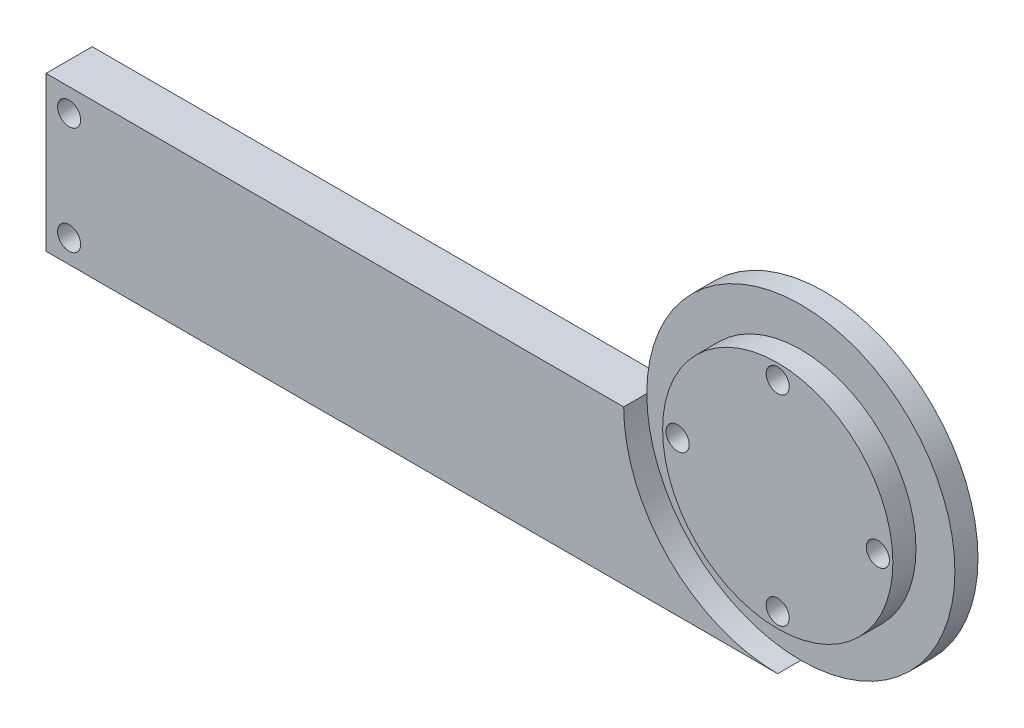
SolidWorks part; units mm, degrees
ref_plane "Plan de face" through (0, 0, 0) normal (0, 0, 1) x (1, 0, 0)
ref_plane "Plan de dessus" through (0, 0, 0) normal (0, 1, 0) x (1, 0, 0)
ref_plane "Plan de droite" through (0, 0, 0) normal (1, 0, 0) x (0, 0, -1)
sketch "Esquisse1" plane through (0, 0, 0) normal (0, 0, 1) x (1, 0, 0)
  line L1 (-45.5828, 28.0993) -> (32.9922, 28.0993)
  line L2 (-45.5828, 28.0993) -> (-45.5828, 8.0993)
  line L3 (-45.5828, 8.0993) -> (32.9922, 8.0993)
  line L4 (32.9922, 28.0993) -> (32.9922, 8.0993)
  circle A0 centre (32.9922, 28.0993) radius 20
  dimension "D3" = 40
  dimension "D1" = 0
  dimension "D2" = 20
  dimension "D4" = 0
extrude "Boss.-Extru.1" add sketch "Esquisse1" along normal blind 6 contours L4 A0 L1 | L1 A0 L4 | A0 L1 L2 L3
sketch "Esquisse4" plane through (0, 0, 6) normal (0, 0, 1) x (1, 0, 0)
  circle A0 centre (32.9922, 28.0993) radius 14.95
  arc A1 (32.9922, 8.0993) -> (12.9922, 28.0993) centre (32.9922, 28.0993) ccw construction
  circle A2 centre (32.9922, 28.0993) radius 20
  dimension "D1" = 0
  dimension "D2" = 29.9
extrude "Enlèv. mat.-Extru.2" cut sketch "Esquisse4" against normal blind 3
sketch "Esquisse5" plane through (0, 0, 6) normal (0, 0, 1) x (1, 0, 0)
  line L0 (-45.5828, 28.0993) -> (12.9922, 28.0993) construction
  line L1 (-45.5828, 8.0993) -> (-62.0028, 8.0993)
  line L2 (-45.5828, 8.0993) -> (-45.5828, 28.0993)
  line L3 (-45.5828, 28.0993) -> (-62.0028, 28.0993)
  line L4 (-62.0028, 8.0993) -> (-62.0028, 28.0993)
  dimension "D1" = 0
  dimension "D2" = 16.42
  dimension "D3" = 20
extrude "Boss.-Extru.2" add sketch "Esquisse5" against normal blind 6
sketch "Esquisse6" plane through (0, 0, 6) normal (0, 0, 1) x (1, 0, 0)
  circle A0 centre (32.9922, 28.0993) radius 13 construction
  circle A1 centre (32.9922, 28.0993) radius 14.95 construction
  circle A2 centre (32.9922, 41.0993) radius 1.5
  circle A3 centre (45.9922, 28.0993) radius 1.5
  circle A4 centre (32.9922, 15.0993) radius 1.5
  circle A5 centre (19.9922, 28.0993) radius 1.5
  dimension "D1" = 0
  dimension "D2" = 26
  dimension "D3" = 3
  dimension "D4" = 3
  dimension "D5" = 3
  dimension "D6" = 3
extrude "Enlèv. mat.-Extru.3" cut sketch "Esquisse6" against normal blind 10
sketch "Esquisse8" plane through (0, 0, 0) normal (0, 0, -1) x (-1, 0, 0)
  circle A0 centre (-32.9922, 28.0993) radius 20
  arc A1 (-12.9922, 28.0993) -> (-32.9922, 8.0993) centre (-32.9922, 28.0993) ccw construction
  circle A2 centre (-32.9922, 28.0993) radius 15
  dimension "D1" = 0
sketch "Esquisse9" plane through (0, 0, 0) normal (0, 0, -1) x (-1, 0, 0)
  line L0 (59.0028, 45.4498) -> (59.0028, -4.8699) construction
  line L1 (62.0028, 28.0993) -> (62.0028, 8.0993) construction
  line L2 (62.0028, 28.0993) -> (-12.9922, 28.0993) construction
  line L3 (62.0028, 8.0993) -> (-32.9922, 8.0993) construction
  circle A0 centre (59.0028, 25.0993) radius 1.5
  circle A1 centre (59.0028, 11.0993) radius 1.5
  dimension "D2" = 3
  dimension "D3" = 3
  dimension "D4" = 3
  dimension "D5" = 3
  dimension "D1" = 3
extrude "Enlèv. mat.-Extru.4" cut sketch "Esquisse9" against normal blind 10
